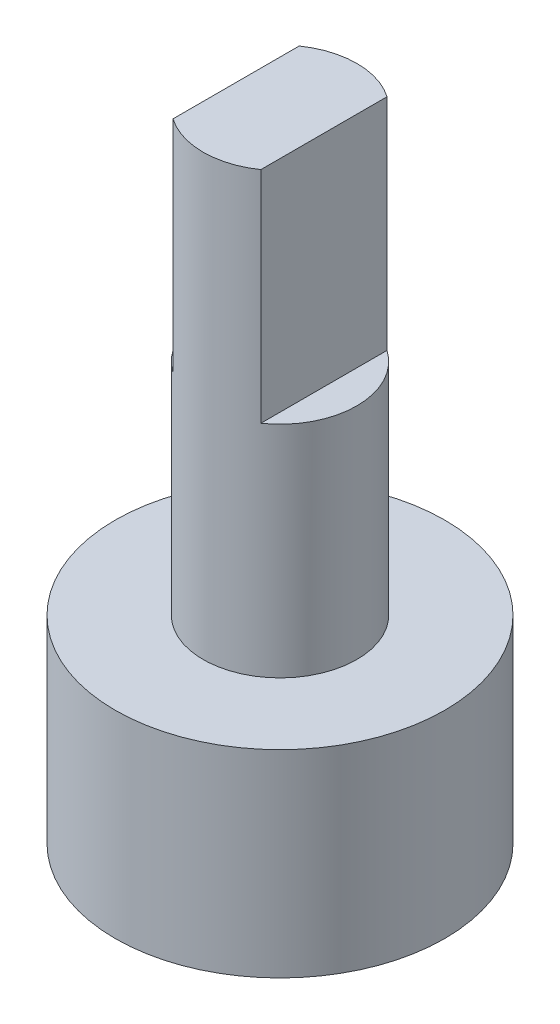
SolidWorks part; units mm, degrees
ref_plane "Front Plane" through (0, 0, 0) normal (0, 0, 1) x (1, 0, 0)
ref_plane "Top Plane" through (0, 0, 0) normal (0, 1, 0) x (1, 0, 0)
ref_plane "Right Plane" through (0, 0, 0) normal (1, 0, 0) x (0, 0, -1)
sketch "Sketch1" plane through (0, 0, 0) normal (0, 1, 0) x (1, 0, 0)
  circle A0 centre (0, 0) radius 1.75
  dimension "D1" = 3.5
extrude "Boss-Extrude1" add sketch "Sketch1" along normal blind 10
sketch "Sketch2" plane through (0, 10, 0) normal (0, 1, 0) x (1, 0, 0)
  line L0 (0, 0) -> (0, 1.9075) construction
  line L1 (-1, 1.4361) -> (-1, -1.4361)
  line L2 (1, 1.4361) -> (1, -1.4361)
  arc A0 (-1, 1.4361) -> (-1, -1.4361) centre (0, 0) ccw
  circle A1 centre (0, 0) radius 1.75 construction
  arc A2 (1, -1.4361) -> (1, 1.4361) centre (0, 0) ccw
  dimension "D1" = 2
extrude "Cut-Extrude1" cut sketch "Sketch2" against normal blind 5
sketch "Sketch3" plane through (0, 0, 0) normal (0, -1, 0) x (1, 0, 0)
  circle A0 centre (0, 0) radius 3.75
  dimension "D1" = 7.5
extrude "Boss-Extrude2" add sketch "Sketch3" along normal blind 4.5
sketch "Sketch4" plane through (0, -4.5, 0) normal (0, -1, 0) x (1, 0, 0)
  circle A0 centre (0, 0) radius 3.25
  dimension "D1" = 6.5
extrude "Cut-Extrude2" cut sketch "Sketch4" against normal blind 2.5
sketch "Sketch5" plane through (0, -2, 0) normal (0, -1, 0) x (1, 0, 0)
  circle A0 centre (0, 0) radius 2.5
  dimension "D1" = 5
extrude "Cut-Extrude3" cut sketch "Sketch5" against normal blind 1
